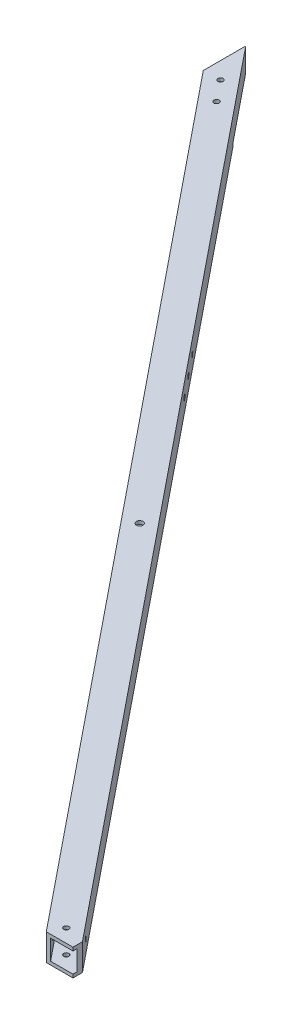
SolidWorks part; units mm, degrees
material "6061-T6 (SS)"
ref_plane "Front Plane" through (0, 0, 0) normal (0, 0, 1) x (1, 0, 0)
ref_plane "Top Plane" through (0, 0, 0) normal (0, 1, 0) x (1, 0, 0)
ref_plane "Right Plane" through (0, 0, 0) normal (1, 0, 0) x (0, 0, -1)
sketch "Sketch1" plane through (0, 0, 0) normal (0, 1, 0) x (1, 0, 0)
  line L0 (0, 0) -> (0, 40.3679)
  line L1 (0, 40.3679) -> (-584.2, 762)
  line L2 (-584.2, 762) -> (-584.2, 721.6321)
  line L3 (-584.2, 721.6321) -> (0, 0)
  line L4 (0, 0) -> (32.68, 0)
  line L5 (0, 40.3679) -> (32.68, 0)
  line L6 (-584.2, 721.6321) -> (-635, 784.3827)
  line L7 (-635, 784.3827) -> (-635, 824.7506)
  line L8 (-635, 824.7506) -> (-584.2, 762)
  dimension "D1" = 584.2
  dimension "D2" = 762
  dimension "D3" = 25.4
  dimension "D4" = 50.8
extrude "Boss-Extrude1" add sketch "Sketch1" along normal blind 25.4 contours L2 L3 L0 L1 | L5 L0 L4 | L8 L7 L6 L2
ref_plane "Plane1" through (12.9383, 0, 15.982) normal (0.6292, 0, 0.7772) x (0, -1, 0)
sketch "Sketch2" plane through (12.9383, 0, 15.982) normal (0.6292, 0, 0.7772) x (0, -1, 0)
  line L0 (-22.225, 22.225) -> (-22.225, 3.175)
  line L1 (-22.225, 3.175) -> (-3.175, 3.175)
  line L2 (-3.175, 3.175) -> (-3.175, 22.225)
  line L3 (-3.175, 22.225) -> (-22.225, 22.225)
  line L4 (0, 0) -> (0, 25.4)
  line L5 (0, 25.4) -> (-25.4, 25.4)
  line L6 (-25.4, 25.4) -> (-25.4, 0)
  line L7 (-25.4, 0) -> (0, 0)
  line L8 (0, 0) -> (0, 25.4)
  line L9 (0, 25.4) -> (-25.4, 25.4)
  line L10 (-25.4, 25.4) -> (-25.4, 0)
  line L11 (-25.4, 0) -> (0, 0)
  dimension "D1" = 0
  dimension "D2" = 3.175
extrude "Cut-Extrude1" cut sketch "Sketch2" against normal through all contours L0 L1 L2 L3
sketch "Sketch3" plane through (0, 25.4, 0) normal (0, 1, 0) x (1, 0, 0)
  line L0 (32.68, 0) -> (-635, 824.7506) construction
  line L1 (0, 0) -> (25.4, 0)
  line L2 (0, 0) -> (0, 40.3679)
  line L3 (0, 40.3679) -> (25.4, 40.3679)
  line L4 (25.4, 0) -> (25.4, 40.3679)
  line L5 (25.4, 40.3679) -> (50.8, 40.3679)
  line L6 (25.4, 40.3679) -> (25.4, 0)
  line L7 (25.4, 0) -> (50.8, 0)
  line L8 (50.8, 40.3679) -> (50.8, 0)
  dimension "D1" = 25.4
extrude "Cut-Extrude4" cut sketch "Sketch3" against normal through all
sketch "Sketch4" plane through (0, 0, 0) normal (0, -1, 0) x (1, 0, 0)
  circle A3 centre (-571.5374, -1019.3063) radius 2.5019
  circle A4 centre (-565.2061, -1008.297) radius 2.5019
  circle A5 centre (6.35, -12.7) radius 2.4892
extrude "Cut-Extrude5" cut sketch "Sketch4" against normal through all
sketch "Sketch6" plane through (0, 0, 0) normal (-0.7772, 0, 0.6292) x (0.6292, 0, 0.7772)
  circle A1 centre (-12.7, 12.7) radius 2.4892
extrude "Cut-Extrude7" cut sketch "Sketch6" against normal through all
sketch "Sketch7" plane through (0, 25.4, 0) normal (0, 1, 0) x (1, 0, 0)
  line L0 (-584.2, 762) -> (-584.2, 381) construction
  line L1 (-584.2, 381) -> (-292.1, 381) construction
  line L2 (-292.1, 381) -> (25.4, 381) construction
  line L3 (25.4, 381) -> (25.4, 0) construction
  line L4 (-308.44, 381) -> (-275.76, 381) construction
  line L5 (25.4, 8.9926) -> (-635, 824.7506) construction
  line L6 (-635, 784.3827) -> (0, 0) construction
  circle A0 centre (-292.1, 381) radius 3.175
  point P13 (-292.1, 381)
  dimension "D1" = 6.35
  dimension "D2" = 609.6
  dimension "D3" = 381
extrude "Cut-Extrude8" cut sketch "Sketch7" against normal through all
sketch "Sketch13" plane through (0, 25.4, 0) normal (0, 1, 0) x (1, 0, 0)
  line L0 (-635, 824.7506) -> (-635, 784.3827)
  line L1 (-635, 784.3827) -> (-584.2, 721.6321)
  line L2 (-635, 784.3827) -> (0, 0) construction
  line L3 (-584.2, 721.6321) -> (-584.2, 762)
  line L4 (25.4, 8.9926) -> (-635, 824.7506) construction
  line L5 (-584.2, 762) -> (-635, 824.7506)
  dimension "D1" = 50.8
extrude "Cut-Extrude12" [suppressed] cut sketch "Sketch13" against normal blind 3.175
sketch "Sketch14" [suppressed] plane through (0, 3.175, 0) normal (0, 1, 0) x (1, 0, 0)
  line L0 (-635, 804.5666) -> (-584.2, 741.816) construction
  line L1 (-635, 819.7046) -> (-635, 789.4287) construction
  line L2 (-584.2, 721.6321) -> (-584.2, 762) construction
  circle A0 centre (-619.018, 784.8249) radius 2.4892
  circle A1 centre (-603.036, 765.0832) radius 2.4892
  dimension "D1" = 25.4
  dimension "D3" = 4.9784
  dimension "D2" = 25.4
extrude "Cut-Extrude13" [suppressed] cut sketch "Sketch14" against normal through all
sketch "Sketch15" plane through (0, 0, 0) normal (0, -1, 0) x (1, 0, 0)
  line L0 (-635, -784.3827) -> (-635, -824.7506)
  line L1 (-635, -824.7506) -> (-584.2, -762)
  line L2 (25.4, -8.9926) -> (-635, -824.7506) construction
  line L3 (-584.2, -762) -> (-584.2, -721.6321)
  line L4 (-635, -784.3827) -> (0, 0) construction
  line L5 (-584.2, -721.6321) -> (-635, -784.3827)
  dimension "D1" = 50.8
extrude "Cut-Extrude14" cut sketch "Sketch15" against normal blind 3.175
sketch "Sketch16" plane through (0, 22.225, 0) normal (0, -1, 0) x (1, 0, 0)
  line L0 (-635, -804.5666) -> (-584.2, -741.816) construction
  line L1 (-635, -789.4287) -> (-635, -819.7046) construction
  line L2 (-584.2, -762) -> (-584.2, -721.6321) construction
  circle A0 centre (-603.036, -765.0832) radius 2.4892
  circle A1 centre (-619.018, -784.8249) radius 2.4892
  dimension "D1" = 25.4
  dimension "D3" = 4.9784
  dimension "D2" = 25.4
extrude "Cut-Extrude15" cut sketch "Sketch16" against normal through all both and the other way through all
sketch "Sketch17" plane through (19.7417, 0, -15.982) normal (0.7772, 0, -0.6292) x (-0.6292, 0, -0.7772)
  line L6 (959.8377, 0) -> (959.8377, 3.175)
  line L7 (959.8377, 0) -> (959.8377, 3.175)
  line L8 (1040.5736, 25.4) -> (-8.9926, 25.4)
  line L9 (-8.9926, 25.4) -> (-8.9926, 0)
  line L10 (-8.9926, 0) -> (959.8377, 0)
  line L11 (1040.5736, 3.175) -> (1040.5736, 25.4)
  line L14 (1040.5736, 25.4) -> (-8.9926, 25.4)
  line L15 (-8.9926, 25.4) -> (-8.9926, 0)
  line L16 (-8.9926, 0) -> (959.8377, 0)
  line L17 (1040.5736, 3.175) -> (1040.5736, 25.4)
  line L18 (959.8377, 3.175) -> (1040.5736, 3.175)
  line L19 (959.8377, 3.175) -> (1040.5736, 3.175)
  circle A0 centre (697.6736, 12.7) radius 2.4892 construction
  circle A1 centre (697.6736, 12.7) radius 2.4892
  circle A2 centre (672.2736, 12.7) radius 2.4892 construction
  circle A3 centre (672.2736, 12.7) radius 2.4892
  circle A4 centre (646.8736, 12.7) radius 2.4892 construction
  circle A5 centre (646.8736, 12.7) radius 2.4892
  dimension "D1" = 0
extrude "Cut-Extrude16" cut sketch "Sketch17" against normal through all contours A5 | A3 | A1
equation "\"Thick\"= \"in\""
